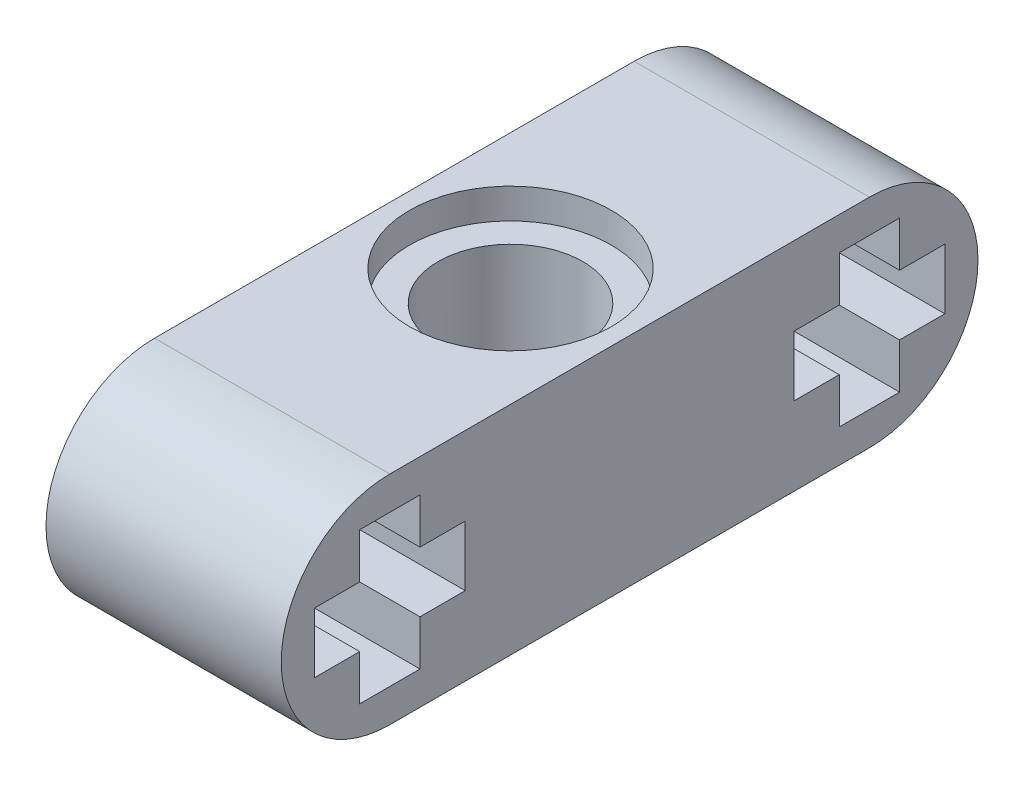
SolidWorks part; units mm, degrees
ref_plane "Front Plane" through (0, 0, 0) normal (0, 0, 1) x (1, 0, 0)
ref_plane "Top Plane" through (0, 0, 0) normal (0, 1, 0) x (1, 0, 0)
ref_plane "Right Plane" through (0, 0, 0) normal (1, 0, 0) x (0, 0, -1)
sketch "Sketch1" plane through (0, 0, 0) normal (1, 0, 0) x (0, 0, -1)
  line L0 (0, 0) -> (-15.9, 0) construction
  line L1 (0, -3.6) -> (-15.9, -3.6)
  line L2 (0, 3.6) -> (-15.9, 3.6)
  line L3 (3.6, -1000) -> (3.6, 49000) construction
  line L4 (-7.95, -1000) -> (-7.95, 49000) construction
  line L5 (-2.5, -1) -> (-1, -1)
  line L6 (-2.5, -1) -> (-2.5, 1)
  line L7 (-2.5, 1) -> (-1, 1)
  line L8 (2.5, -1) -> (2.5, 1)
  line L9 (-13.4, -1) -> (-13.4, 1)
  line L10 (-13.4, 1) -> (-14.9, 1)
  line L11 (1, -2.5) -> (-1, -2.5)
  line L12 (1, -2.5) -> (1, -1)
  line L13 (1, 2.5) -> (-1, 2.5)
  line L14 (-1, -2.5) -> (-1, -1)
  line L17 (1, 1) -> (2.5, 1)
  line L20 (1, 1) -> (1, 2.5)
  line L22 (1, -1) -> (2.5, -1)
  line L23 (-1, 1) -> (-1, 2.5)
  line L24 (-14.9, 1) -> (-14.9, 2.5)
  line L25 (-16.9, 2.5) -> (-14.9, 2.5)
  line L26 (-16.9, 1) -> (-16.9, 2.5)
  line L27 (-16.9, 1) -> (-18.4, 1)
  line L28 (-18.4, -1) -> (-18.4, 1)
  line L29 (-16.9, -1) -> (-18.4, -1)
  line L30 (-16.9, -2.5) -> (-16.9, -1)
  line L31 (-16.9, -2.5) -> (-14.9, -2.5)
  line L32 (-14.9, -2.5) -> (-14.9, -1)
  line L33 (-13.4, -1) -> (-14.9, -1)
  arc A0 (0, -3.6) -> (0, 3.6) centre (0, 0) ccw
  arc A1 (-15.9, 3.6) -> (-15.9, -3.6) centre (-15.9, 0) ccw
  circle A2 centre (0.1, 0) radius 3.25 construction
  circle A3 centre (-16, 0) radius 3.25 construction
  point P3 (-7.95, 0)
  point P8 (3.6, 0)
  point P9 (-19.5, 0)
  point P14 (0, 0)
  point P19 (0, 0)
  point P44 (-18.4, 0)
  dimension "D1" = 23.1
  dimension "D2" = 20.9
  dimension "D6" = 5
  dimension "D8" = 2
extrude "Boss-Extrude1" add sketch "Sketch1" along normal blind 7.8
sketch "Sketch2" plane through (7.8, 0, 0) normal (1, 0, 0) x (0, 0, -1)
  line L0 (-19.5, 0) -> (3.6, 0) construction
  line L1 (-7.95, -1000) -> (-7.95, 49000) construction
  line L2 (-3.5, -1000) -> (-3.5, 49000) construction
  line L3 (-2.5, 1) -> (-2.5, -1) construction
  arc A0 (-15.9, 3.6) -> (-15.9, -3.6) centre (-15.9, 0) ccw construction
  arc A1 (0, -3.6) -> (0, 3.6) centre (0, 0) ccw construction
  circle A2 centre (0, 0) radius 3.5 construction
  circle A3 centre (-15.9, 0) radius 3.5 construction
  point P11 (-7.95, 0)
  dimension "D1" = 1
sketch "Sketch3" plane through (0, 3.6, 0) normal (0, 1, 0) x (1, 0, 0)
  line L0 (3.9, -996.4) -> (3.9, 49003.6) construction
  line L1 (7.8, 3.6) -> (0, 3.6) construction
  line L2 (-996.1, -19.5) -> (49003.9, -19.5) construction
  line L3 (0, -19.5) -> (7.8, -19.5) construction
  line L4 (-996.1, 3.6) -> (49003.9, 3.6) construction
  line L6 (0, -1001.4334) -> (0, 48998.5666) construction
  line L8 (7.8, -1002.0171) -> (7.8, 48997.9829) construction
  circle A0 centre (3.9, -8) radius 2.4
  circle A1 centre (3.9, -8) radius 3
  circle A2 centre (3.9, -8) radius 3.6
  point P5 (3.9, 3.6)
  point P6 (3.9, -8)
  point P10 (3.9, -19.5)
  dimension "D2" = 4.8
  dimension "D3" = 0.6
  dimension "D4" = 7.2
  dimension "D1" = 11.6
extrude "Cut-Extrude1" cut sketch "Sketch3" against normal blind 7.2 contours A0
sketch "Sketch5" plane through (0, 3.6, 0) normal (0, 1, 0) x (1, 0, 0)
  line L0 (-996.1, -10.4) -> (49003.9, -10.4) construction
sketch "Sketch6" plane through (0, 3.6, 0) normal (0, 1, 0) x (1, 0, 0)
  circle A0 centre (3.9, -8) radius 2.4
  circle A1 centre (3.9, -8) radius 3.3454
  circle M3 centre (3.9, -8) radius 2.4
  dimension "D1" = 4.8
  dimension "D2" = 6.6908
extrude "Cut-Extrude3" cut sketch "Sketch6" against normal blind 1 contours A1 M3
ref_plane "Plane5" through (0, 0, 0) normal (0, -1, 0) x (-1, 0, 0)
mirror "Mirror1" about plane through (0, 0, 0) normal (0, -1, 0) of "Cut-Extrude3"
